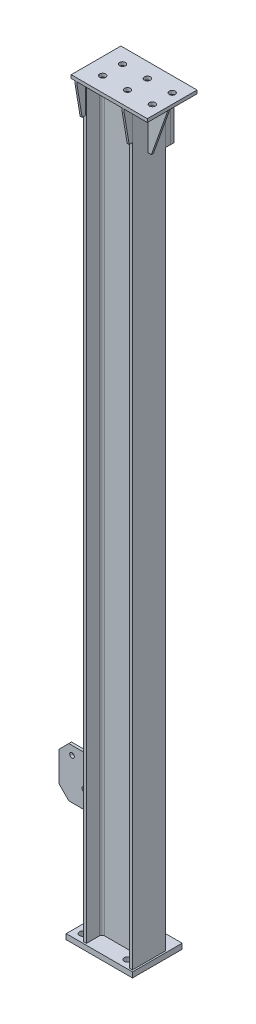
SolidWorks part; units mm, degrees
material "普通碳钢"
ref_plane "前视基准面" through (0, 0, 0) normal (0, 0, 1) x (1, 0, 0)
ref_plane "上视基准面" through (0, 0, 0) normal (0, 1, 0) x (1, 0, 0)
ref_plane "右视基准面" through (0, 0, 0) normal (1, 0, 0) x (0, 0, -1)
sketch "草图1" plane through (0, 0, 0) normal (1, 0, 0) x (0, 0, -1)
  line L0 (0, 0) -> (0, 2263)
  dimension "D1" = 2263
other "H型钢 HM150×100(5)"
ref_plane "基准面1" through (0, 0, 0) normal (0, 1, 0) x (0, 0, 1)
sketch "草图11" plane through (0, 0, 0) normal (0, 1, 0) x (0, 0, 1)
  line L0 (-50, -74) -> (50, -74)
  line L1 (50, -74) -> (50, -65)
  line L2 (50, -65) -> (11, -65)
  line L3 (3, -57) -> (3, 57)
  line L4 (11, 65) -> (50, 65)
  line L5 (50, 65) -> (50, 74)
  line L6 (50, 74) -> (-50, 74)
  line L7 (0, 74) -> (0, -74) construction
  line L11 (0, 60) -> (0, 74) construction
  line L14 (-50, -74) -> (-50, -65)
  line L15 (-50, -65) -> (-11, -65)
  line L16 (-3, -57) -> (-3, 57)
  line L17 (-11, 65) -> (-50, 65)
  line L18 (-50, 65) -> (-50, 74)
  arc A2 (11, -65) -> (3, -57) centre (11, -57) cw
  arc A3 (3, 57) -> (11, 65) centre (11, 57) cw
  arc A5 (-11, -65) -> (-3, -57) centre (-11, -57) ccw
  arc A6 (-3, 57) -> (-11, 65) centre (-11, 57) ccw
  point P2 (0, 0)
  point P38 (0, 0)
  point P39 (50, 74)
  point P40 (50, -74)
  point P41 (-50, -74)
  dimension "D8" = 8
  dimension "D1" = 6
  dimension "D2" = 9
  dimension "D3" = 148
  dimension "D4" = 100
  dimension "D9" = 0
sketch "草图12" plane through (0, 0, 0) normal (0, -1, 0) x (1, 0, 0)
  line L2 (79, 55) -> (79, -95)
  line L3 (79, -95) -> (-121, -95)
  line L4 (-121, 55) -> (-121, -95)
  line L5 (79, 55) -> (-121, 55)
  line L6 (74, 50) -> (74, -50) construction
  line L8 (-74, 50) -> (-65, 50) construction
  dimension "D1" = 200
  dimension "D2" = 5
  dimension "D3" = 5
  dimension "D4" = 150
extrude "凸台-拉伸1" add sketch "草图12" along normal blind 16 separate body contours L2 L3 L4 L5
sketch "草图13" plane through (0, 2263, 0) normal (0, 1, 0) x (1, 0, 0)
  line L1 (144, -75) -> (-86, -75)
  line L2 (144, -75) -> (144, 75)
  line L3 (144, 75) -> (-86, 75)
  line L4 (-86, -75) -> (-86, 75)
  line L5 (-74, -50) -> (-65, -50) construction
  line L6 (-74, 50) -> (-74, -50) construction
  dimension "D1" = 230
  dimension "D2" = 150
  dimension "D3" = 12
  dimension "D4" = 25
extrude "凸台-拉伸2" add sketch "草图13" along normal blind 10 separate body
sketch "草图14" plane through (0, 2273, 0) normal (0, 1, 0) x (1, 0, 0)
  line L0 (144, 0) -> (-86, 0) construction
  line L2 (144, -75) -> (144, 75) construction
  line L3 (-86, 75) -> (-86, -75) construction
  line L4 (114, -75) -> (114, 75) construction
  line L5 (-86, -75) -> (144, -75) construction
  line L6 (144, 75) -> (-86, 75) construction
  line L7 (39, -75) -> (39, 75) construction
  line L8 (-36, -75) -> (-36, 75) construction
  line L9 (144, -30) -> (-86, -30) construction
  line L10 (144, 30) -> (-86, 30) construction
  circle A0 centre (114, 30) radius 9
  circle A1 centre (114, -30) radius 9
  circle A2 centre (39, -30) radius 9
  circle A3 centre (39, 30) radius 9
  circle A4 centre (-36, 30) radius 9
  circle A5 centre (-36, -30) radius 9
  dimension "D6" = 18
  dimension "D1" = 30
  dimension "D2" = 75
  dimension "D3" = 75
  dimension "D4" = 30
  dimension "D5" = 30
extrude "切除-拉伸1" cut sketch "草图14" against normal up to next (10 mm away)
sketch "草图16" plane through (-74, 0, 0) normal (-1, 0, 0) x (0, 0, 1)
  line L0 (-50, 0) -> (50, 0) construction
  line L1 (-4, 300) -> (4, 300)
  line L2 (-4, 300) -> (-4, 450)
  line L3 (-4, 450) -> (4, 450)
  line L4 (4, 300) -> (4, 450)
  line L5 (50, 2263) -> (50, 0) construction
  dimension "D1" = 150
  dimension "D2" = 300
  dimension "D3" = 8
  dimension "D4" = 46
extrude "凸台-拉伸4" add sketch "草图16" along normal blind 120 separate body
chamfer "倒角1" distance 30 angle 45 2 edges at (-194, 300, 0) (-194, 450, 0)
sketch "草图17" plane through (0, 0, 4) normal (0, 0, 1) x (1, 0, 0)
  line L0 (-90, 300) -> (-187.5514, 487.3945) construction
  line L1 (-164, 300) -> (-74, 300) construction
  line L2 (-74, 300) -> (-74, 450) construction
  line L3 (-81.4292, 353) -> (-217.3439, 353) construction
  line L4 (-216.0363, 301.7521) -> (-117.5901, 353) construction
  line L5 (-252.9762, 372.713) -> (-154.5299, 423.9609) construction
  circle A0 centre (-154.5299, 423.9609) radius 7
  circle A1 centre (-117.5901, 353) radius 7
  dimension "D5" = 14
  dimension "D6" = 14
  dimension "D1" = 62.5
  dimension "D2" = 16
  dimension "D3" = 53
  dimension "D4" = 80
extrude "切除-拉伸2" cut sketch "草图17" against normal up to next (8 mm away)
sketch "草图18" plane through (0, 0, -3) normal (0, 0, -1) x (-1, 0, 0)
  line L0 (-74, 2263) -> (-74, 2113)
  line L1 (-74, 2113) -> (-84, 2113)
  line L2 (-84, 2113) -> (-134, 2253)
  line L3 (-134, 2253) -> (-134, 2263)
  line L4 (-134, 2263) -> (-74, 2263)
  line L5 (-74, 2263) -> (-74, 0) construction
  line L6 (-144, 2263) -> (86, 2263) construction
  dimension "D1" = 60
  dimension "D2" = 10
  dimension "D3" = 10
  dimension "D4" = 150
extrude "凸台-拉伸5" add sketch "草图18" against normal up to surface (6 mm away) separate body up to face at (0, 1131.5, 3)
sketch "草图19" plane through (74, 0, 0) normal (1, 0, 0) x (0, 0, -1)
  line L0 (-50, 2263) -> (-75, 2263)
  line L1 (-75, 2263) -> (-75, 2253)
  line L2 (-75, 2253) -> (-60, 2163)
  line L3 (-60, 2163) -> (-50, 2163)
  line L4 (-50, 2263) -> (-50, 0) construction
  line L5 (-50, 2163) -> (-50, 2263)
  line L6 (-75, 2273) -> (-75, 2263) construction
  line L7 (50, 2263) -> (65, 2263)
  line L8 (50, 2263) -> (50, 0) construction
  line L9 (65, 2263) -> (65, 2100)
  line L11 (65, 2100) -> (50, 2100)
  line L12 (50, 2100) -> (50, 2263)
  point P25 (57.5, 2263)
  dimension "D1" = 10
  dimension "D2" = 10
  dimension "D3" = 100
  dimension "D4" = 15
  dimension "D5" = 163
extrude "凸台-拉伸6" add sketch "草图19" against normal blind 6 separate body
sketch "草图20" plane through (-74, 0, 0) normal (-1, 0, 0) x (0, 0, 1)
  line L5 (50, 2263) -> (50, 2163)
  line L6 (50, 2163) -> (60, 2163)
  line L7 (60, 2163) -> (75, 2253)
  line L8 (75, 2253) -> (75, 2263)
  line L9 (75, 2263) -> (50, 2263)
  line L10 (50, 2263) -> (50, 2163)
  line L11 (50, 2163) -> (60, 2163)
  line L12 (60, 2163) -> (75, 2253)
  line L13 (75, 2253) -> (75, 2263)
  line L14 (75, 2263) -> (50, 2263)
  line L21 (-50, 2100) -> (-50, 2263)
  line L22 (-50, 2263) -> (-65, 2263)
  line L23 (-65, 2263) -> (-65, 2100)
  line L25 (-65, 2100) -> (-50, 2100)
  line L26 (-50, 2100) -> (-50, 2263)
  line L27 (-50, 2263) -> (-65, 2263)
  line L28 (-65, 2263) -> (-65, 2100)
  line L30 (-65, 2100) -> (-50, 2100)
  dimension "D2" = 0
  dimension "D1" = 0
extrude "凸台-拉伸7" add sketch "草图20" against normal blind 6 separate body
sketch "草图21" plane through (74, 0, 0) normal (1, 0, 0) x (0, 0, -1)
  line L0 (50, 2100) -> (65, 2100) construction
  line L1 (65, 2100) -> (75, 2100)
  line L2 (65, 2100) -> (65, 2248)
  line L3 (65, 2248) -> (75, 2248)
  line L4 (75, 2100) -> (75, 2248)
  line L5 (65, 2100) -> (65, 2263) construction
  line L7 (65, 2263) -> (50, 2263) construction
  dimension "D1" = 10
  dimension "D2" = 15
extrude "凸台-拉伸8" add sketch "草图21" against normal up to surface (148 mm away) separate body up to face at (-74, 2181.5, -57.5)
sketch "草图22" plane through (0, 0, 0) normal (0, 1, 0) x (1, 0, 0)
  line L0 (39, 70) -> (-96, 70) construction
  line L1 (-96, 70) -> (-96, -30) construction
  line L2 (-96, -30) -> (39, -30) construction
  line L3 (39, -30) -> (39, 70) construction
  line L5 (-121, -55) -> (-121, 95) construction
  line L6 (79, 95) -> (-121, 95) construction
  circle A0 centre (-96, -30) radius 10
  circle A1 centre (39, -30) radius 10
  circle A2 centre (-96, 70) radius 10
  circle A3 centre (39, 70) radius 10
  dimension "D3" = 20
  dimension "D1" = 135
  dimension "D2" = 100
  dimension "D4" = 25
  dimension "D5" = 25
extrude "切除-拉伸3" cut sketch "草图22" against normal up to next (16 mm away)
